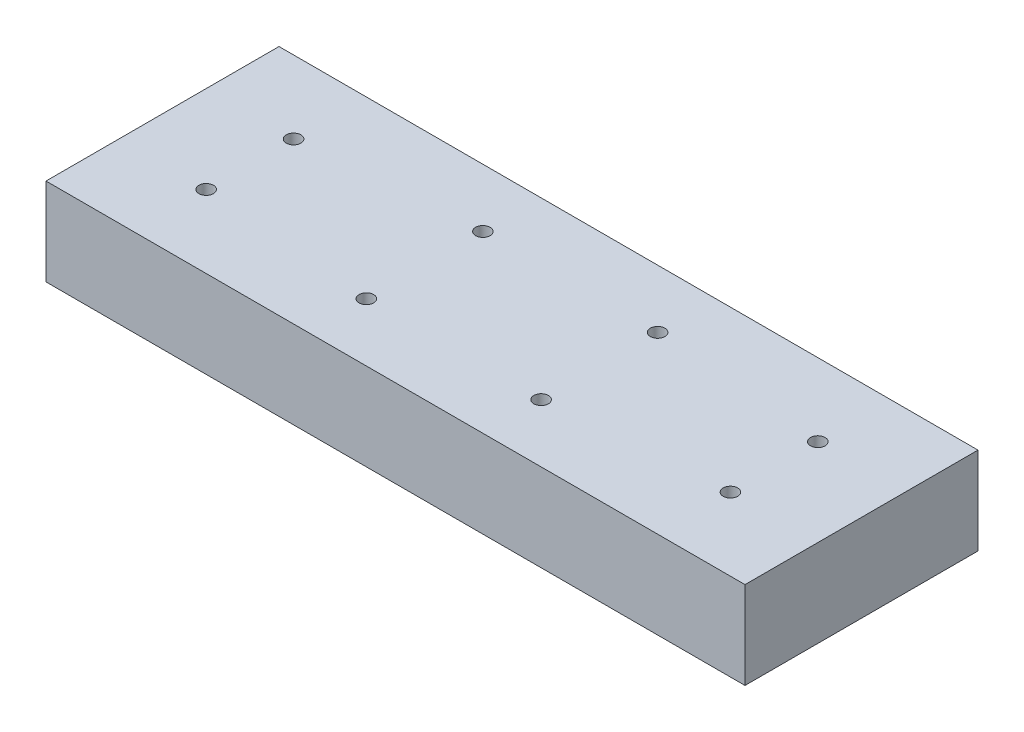
SolidWorks part; units mm, degrees
material "Oak"
ref_plane "Front Plane" through (0, 0, 0) normal (0, 0, 1) x (1, 0, 0)
ref_plane "Top Plane" through (0, 0, 0) normal (0, 1, 0) x (1, 0, 0)
ref_plane "Right Plane" through (0, 0, 0) normal (1, 0, 0) x (0, 0, -1)
sketch "Sketch1" plane through (0, 0, 0) normal (0, 1, 0) x (1, 0, 0)
  line L0 (57.15, -12.7) -> (95.25, -12.7) construction
  line L1 (0, 0) -> (152.4, 0)
  line L2 (0, 0) -> (0, -50.8)
  line L3 (0, -50.8) -> (152.4, -50.8)
  line L4 (152.4, 0) -> (152.4, -50.8)
  line L5 (95.25, -12.7) -> (95.25, -38.1) construction
  line L7 (19.05, -34.925) -> (133.35, -34.925) construction
  line L8 (19.05, -34.925) -> (19.05, -15.875) construction
  line L9 (19.05, -15.875) -> (133.35, -15.875) construction
  line L10 (133.35, -34.925) -> (133.35, -15.875) construction
  circle A0 centre (57.15, -12.7) radius 1.5875
  circle A1 centre (57.15, -38.1) radius 1.5875
  circle A2 centre (95.25, -12.7) radius 1.5875
  circle A3 centre (95.25, -38.1) radius 1.5875
  circle A4 centre (19.05, -15.875) radius 1.5875
  circle A5 centre (19.05, -34.925) radius 1.5875
  circle A6 centre (133.35, -15.875) radius 1.5875
  circle A7 centre (133.35, -34.925) radius 1.5875
  point P13 (76.2, -12.7)
  point P14 (76.2, 0)
  point P15 (95.25, -25.4)
  point P16 (152.4, -25.4)
  point P17 (19.05, -25.4)
  point P23 (76.2, -34.925)
  dimension "D3" = 3.175
  dimension "D4" = 38.1
  dimension "D6" = 19.05
  dimension "D1" = 50.8
  dimension "D2" = 152.4
  dimension "D5" = 25.4
  dimension "D7" = 114.3
extrude "Boss-Extrude1" add sketch "Sketch1" along normal blind 19.05
sketch "Sketch2" plane through (0, 0, 0) normal (0, -1, 0) x (-1, 0, 0)
  circle A0 centre (-19.05, -34.925) radius 5.5563
  circle A1 centre (-19.05, -15.875) radius 5.5562
  circle A2 centre (-57.15, -38.1) radius 5.5562
  circle A3 centre (-57.15, -12.7) radius 5.5562
  circle A4 centre (-95.25, -38.1) radius 5.5563
  circle A5 centre (-95.25, -12.7) radius 5.5563
  circle A6 centre (-133.35, -15.875) radius 5.5563
  circle A7 centre (-133.35, -34.925) radius 5.5563
  dimension "D1" = 11.1125
extrude "Cut-Extrude1" cut sketch "Sketch2" against normal blind 6.35
